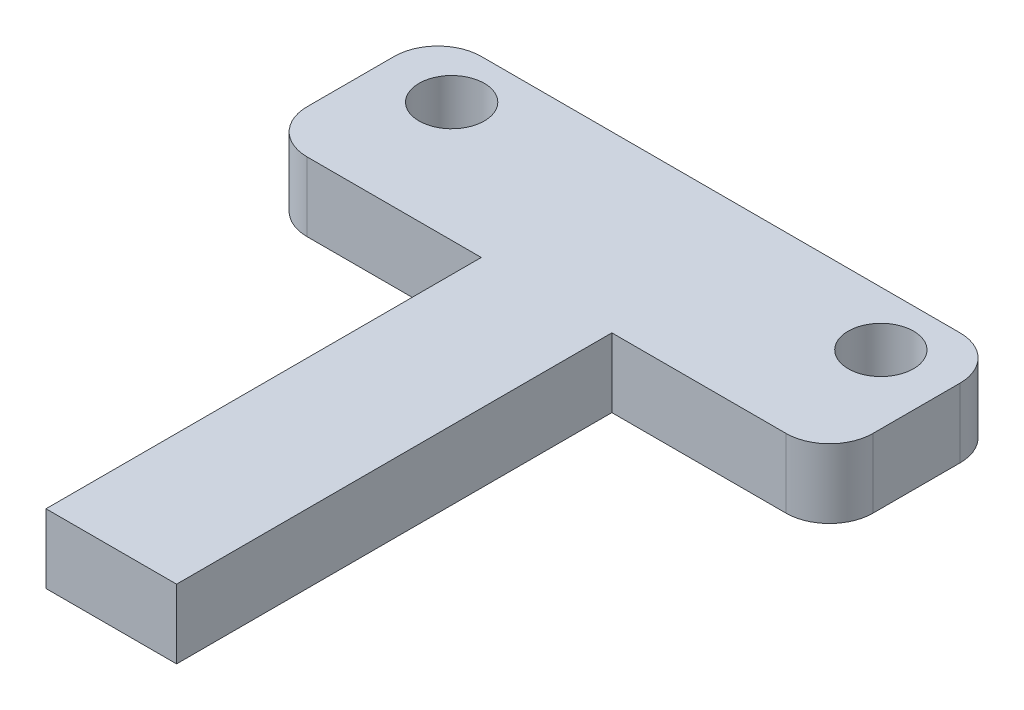
SolidWorks part; units mm, degrees
ref_plane "前视基准面" through (0, 0, 0) normal (0, 0, 1) x (1, 0, 0)
ref_plane "上视基准面" through (0, 0, 0) normal (0, 1, 0) x (1, 0, 0)
ref_plane "右视基准面" through (0, 0, 0) normal (1, 0, 0) x (0, 0, -1)
other "Configuration Table"
sketch "草图1" plane through (0, 0, 0) normal (0, 1, 0) x (1, 0, 0)
  line L0 (0, 0) -> (41.0539, 0) construction
  line L1 (-11, 4) -> (11, 4)
  line L2 (-13, 2) -> (-13, -2)
  line L3 (-11, -4) -> (-3, -4)
  line L4 (13, 2) -> (13, -2)
  line L5 (-13, 4) -> (13, -4) construction
  line L6 (-13, -4) -> (13, 4) construction
  line L7 (0, 0) -> (0, 18.5654) construction
  line L8 (-3, -4) -> (-3, -24)
  line L9 (-3, -24) -> (3, -24)
  line L10 (3, -4) -> (3, -24)
  line L11 (3, -4) -> (11, -4)
  circle A0 centre (-9.86, 1.5) radius 1.5
  circle A1 centre (9.86, 1.5) radius 1.5
  arc A2 (-13, -2) -> (-11, -4) centre (-11, -2) ccw
  arc A3 (11, -4) -> (13, -2) centre (11, -2) ccw
  arc A4 (11, 4) -> (13, 2) centre (11, 2) cw
  arc A5 (-11, 4) -> (-13, 2) centre (-11, 2) ccw
  point P0 (0, 0)
  point P14 (0, -24)
  dimension "D5" = 3
  dimension "D8" = 2
  dimension "D1" = 3
  dimension "D2" = 20
  dimension "D3" = 26
  dimension "D4" = 8
  dimension "D6" = 2.5
  dimension "D7" = 19.72
extrude "凸台-拉伸1" add sketch "草图1" along normal blind 3.175
